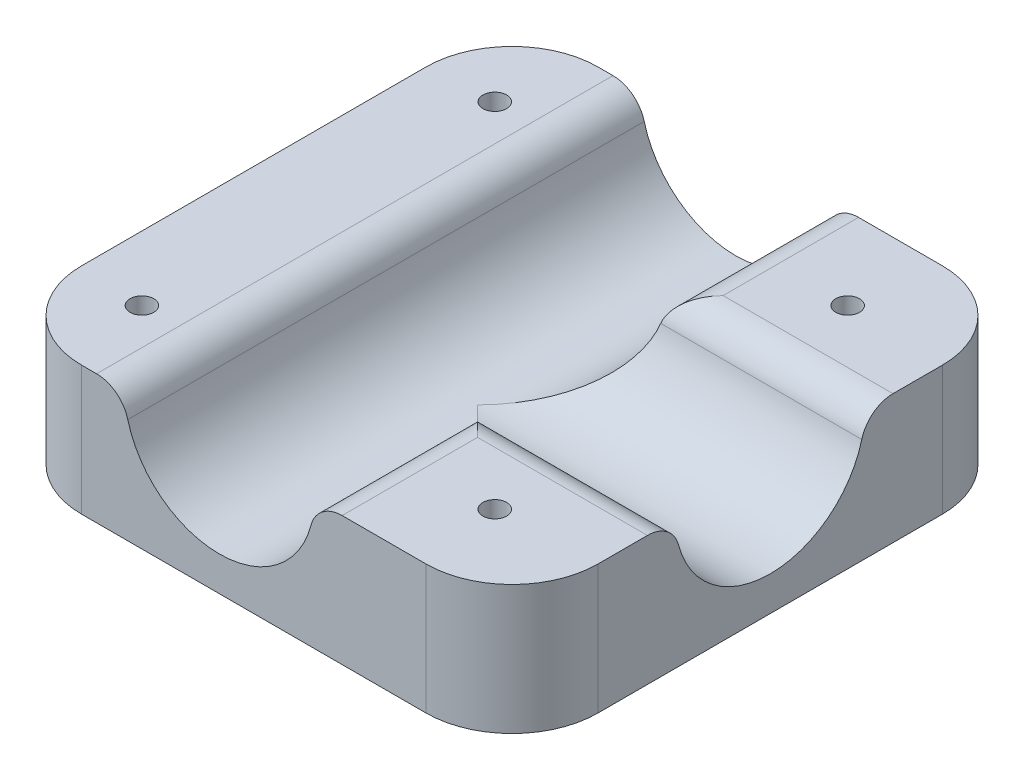
SolidWorks part; units mm, degrees
ref_plane "Front Plane" through (0, 0, 0) normal (0, 0, 1) x (1, 0, 0)
ref_plane "Top Plane" through (0, 0, 0) normal (0, 1, 0) x (1, 0, 0)
ref_plane "Right Plane" through (0, 0, 0) normal (1, 0, 0) x (0, 0, -1)
sketch "Sketch1" plane through (0, 0, 0) normal (0, 1, 0) x (1, 0, 0)
  line L5 (19.05, 0) -> (0, 0) construction
  line L6 (0, 0) -> (76.2, 0)
  line L7 (0, 0) -> (0, 76.2)
  line L8 (0, 76.2) -> (76.2, 76.2)
  line L9 (76.2, 0) -> (76.2, 76.2)
  line L10 (19.05, 76.2) -> (46.99, 76.2)
  line L11 (19.05, 76.2) -> (19.05, 0)
  line L12 (19.05, 0) -> (46.99, 0)
  line L13 (46.99, 76.2) -> (46.99, 0)
  line L14 (76.2, 24.13) -> (46.99, 24.13)
  line L15 (76.2, 24.13) -> (76.2, 52.07)
  line L16 (76.2, 52.07) -> (46.99, 52.07)
  line L17 (46.99, 24.13) -> (46.99, 52.07)
  line L18 (9.525, 0) -> (9.525, 76.2) construction
  line L19 (76.2, 76.2) -> (46.99, 76.2) construction
  line L20 (61.595, 76.2) -> (61.595, 52.07) construction
  line L21 (61.595, 24.13) -> (61.595, 0) construction
  line L22 (9.525, 64.135) -> (61.595, 64.135) construction
  line L23 (9.525, 12.065) -> (61.595, 12.065) construction
  circle A1 centre (61.595, 12.065) radius 1.75
  circle A2 centre (61.595, 64.135) radius 1.75
  circle A3 centre (9.525, 64.135) radius 1.75
  circle A4 centre (9.525, 12.065) radius 1.75
  point P14 (76.2, 38.1)
  dimension "D4" = 76.2
  dimension "D6" = 3.5
  dimension "D1" = 27.94
  dimension "D2" = 27.94
  dimension "D3" = 19.05
  dimension "D5" = 76.2
extrude "Boss-Extrude2" add sketch "Sketch1" along normal blind 19.05 contours L11 L8 L7 L6 A4 A3 | L13 L8 L11 L6 | L16 L9 L8 L13 A2 | L9 L16 L13 L14 | L9 L14 L13 L6 A1
sketch "Sketch3" plane through (0, 0, 0) normal (0, 0, 1) x (1, 0, 0)
  line L1 (19.05, 0) -> (19.05, 19.05) construction
  line L2 (19.05, 0) -> (0, 0) construction
  line L3 (0, 0) -> (76.2, 0) construction
  line L4 (0, 19.05) -> (76.2, 19.05) construction
  line L5 (46.99, 0) -> (46.99, 19.05) construction
  line L6 (19.05, 0) -> (46.99, 0) construction
  line L7 (9.525, 0) -> (61.595, 0) construction
  line L8 (19.05, 19.05) -> (46.99, 19.05) construction
  circle A0 centre (33.02, 19.05) radius 13.97
  dimension "D1" = 27.94
extrude "Cut-Extrude2" cut sketch "Sketch3" against normal through all
sketch "Sketch4" plane through (76.2, 0, 0) normal (1, 0, 0) x (0, 0, -1)
  line L0 (24.13, 0) -> (24.13, 19.05) construction
  line L1 (0, 19.05) -> (76.2, 19.05) construction
  line L2 (52.07, 0) -> (52.07, 19.05) construction
  line L3 (24.13, 19.05) -> (52.07, 19.05) construction
  circle A0 centre (38.1, 19.05) radius 13.97
  dimension "D1" = 27.94
extrude "Cut-Extrude3" cut sketch "Sketch4" against normal up to next
fillet "Fillet1" radius 4.7625 5 edges at (46.99, 19.05, -12.065) (61.595, 19.05, -24.13) (61.595, 19.05, -52.07) (46.99, 19.05, -64.135) (19.05, 19.05, -38.1)
fillet "Fillet2" radius 12.7 4 edges at (76.2, 9.525, -76.2) (0, 9.525, -76.2) (0, 9.525, 0) (76.2, 9.525, 0)
